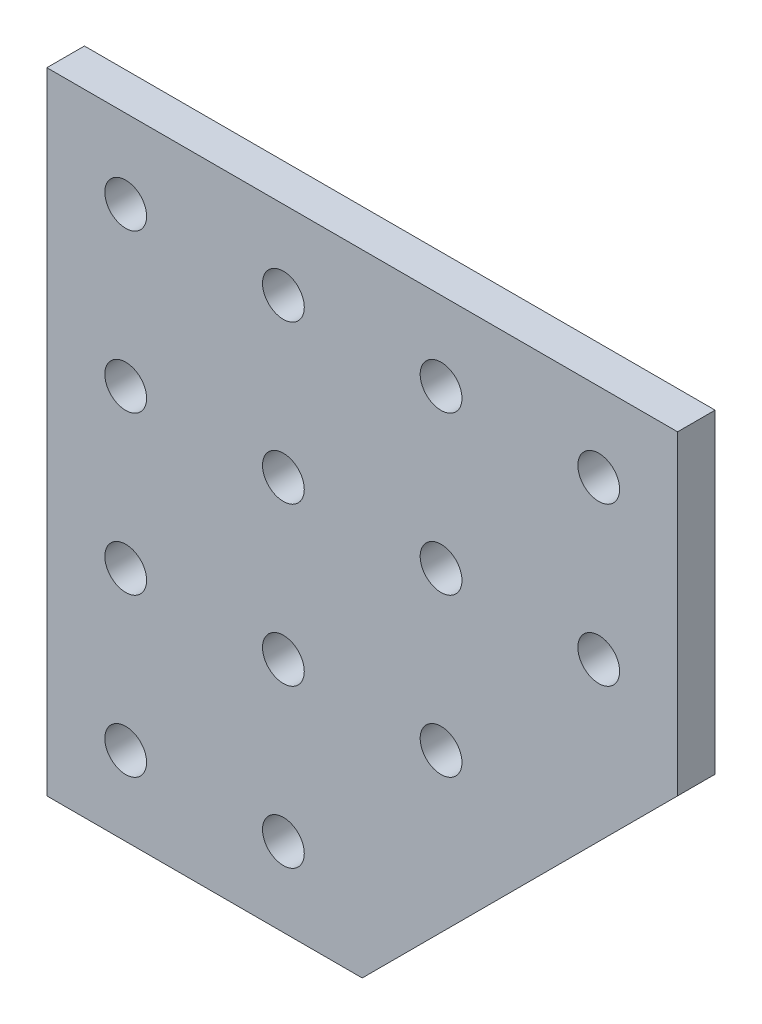
SolidWorks part; units mm, degrees
ref_plane "Front Plane" through (0, 0, 0) normal (0, 0, 1) x (1, 0, 0)
ref_plane "Top Plane" through (0, 0, 0) normal (0, 1, 0) x (1, 0, 0)
ref_plane "Right Plane" through (0, 0, 0) normal (1, 0, 0) x (0, 0, -1)
sketch "Sketch1" plane through (0, 0, 0) normal (0, 0, 1) x (1, 0, 0)
  line L0 (40, 0) -> (40, 80)
  line L1 (0, 0) -> (40, 0)
  line L2 (0, 0) -> (0, 80)
  line L3 (0, 80) -> (80, 80)
  line L4 (80, 40) -> (80, 80)
  line L5 (80, 40) -> (0, 40)
  line L6 (40, 0) -> (80, 40)
  dimension "D1" = 80
  dimension "D2" = 80
extrude "Boss-Extrude1" add sketch "Sketch1" along normal blind 4.7625 contours L0 L5 L2 L1 | L5 L0 L3 L2 | L5 L4 L3 L0 | L0 L6 L5
hole_wizard "M5 Clearance Hole1" positions "Sketch2" profile "Sketch3" hole size "M5" standard "ANSI Metric"
sketch "Sketch2" plane through (0, 0, 4.7625) normal (0, 0, 1) x (1, 0, 0)
  line L0 (0, 80) -> (80, 80) construction
  line L1 (0, 0) -> (0, 80) construction
  point P0 (10, 70)
  point P21 (30, 70)
  point P22 (50, 70)
  point P23 (70, 70)
  point P24 (30, 50)
  point P25 (50, 50)
  point P26 (70, 50)
  point P27 (30, 30)
  point P28 (50, 30)
  point P29 (70, 30) [skipped]
  point P30 (30, 10)
  point P31 (50, 10) [skipped]
  point P32 (70, 10) [skipped]
  point P33 (10, 50)
  point P34 (10, 30)
  point P35 (10, 10)
  dimension "D1" = 10
  dimension "D2" = 10
  dimension "D3" = 4
  dimension "D4" = 4
sketch "Sketch3" plane through (10, 70, 4.7625) normal (1, 0, 0) x (0, -1, 0)
  line L0 (0, 0) -> (0, 4.7625)
  line L1 (0, 4.7625) -> (2.65, 4.7625)
  line L2 (2.65, 4.7625) -> (2.65, 0)
  line L5 (2.65, 0) -> (0, 0)
  line L11 (0, -6.35) -> (0, 107.95) construction
  dimension "Thru Hole Dia." = 5.3
  dimension "Thru Hole Depth" = 4.7625
sketch "Sketch4" plane through (0, 0, 0) normal (-1, 0, 0) x (0, 0, 1)
  line L4 (0, 80) -> (0, 0)
  line L5 (0, 0) -> (4.7625, 0)
  line L6 (4.7625, 0) -> (4.7625, 80)
  line L7 (4.7625, 80) -> (0, 80)
  line L8 (0, 80) -> (0, 0)
  line L9 (0, 0) -> (4.7625, 0)
  line L10 (4.7625, 0) -> (4.7625, 80)
  line L11 (4.7625, 80) -> (0, 80)
  dimension "D1" = 0
extrude "Boss-Extrude2" [suppressed] add sketch "Sketch4" along normal blind 3
fillet "Fillet1" [suppressed] radius 1
